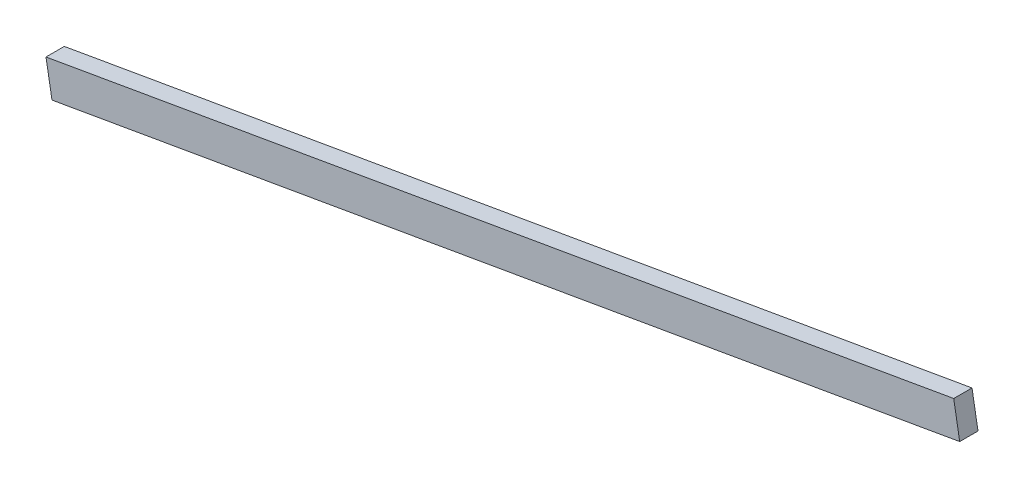
SolidWorks part; units mm, degrees
ref_plane "Front" through (0, 0, 0) normal (0, 0, 1) x (1, 0, 0)
ref_plane "Top" through (0, 0, 0) normal (0, 1, 0) x (1, 0, 0)
ref_plane "Right" through (0, 0, 0) normal (1, 0, 0) x (0, 0, -1)
sketch "Sketch1" plane through (0, 0, 0) normal (0, 0, 1) x (1, 0, 0)
  line L0 (-1.7432, -160.226) -> (262.8213, -114.1507)
  line L1 (-1.7432, -160.226) -> (0, -170.2354)
  line L2 (262.8213, -114.1507) -> (264.5645, -124.1601)
  line L3 (0, -170.2354) -> (264.5645, -124.1601)
  point P0 (0, -170.2354)
  dimension "D1" = 10.16
extrude "Boss-Extrude1" add sketch "Sketch1" along normal blind 5.334
